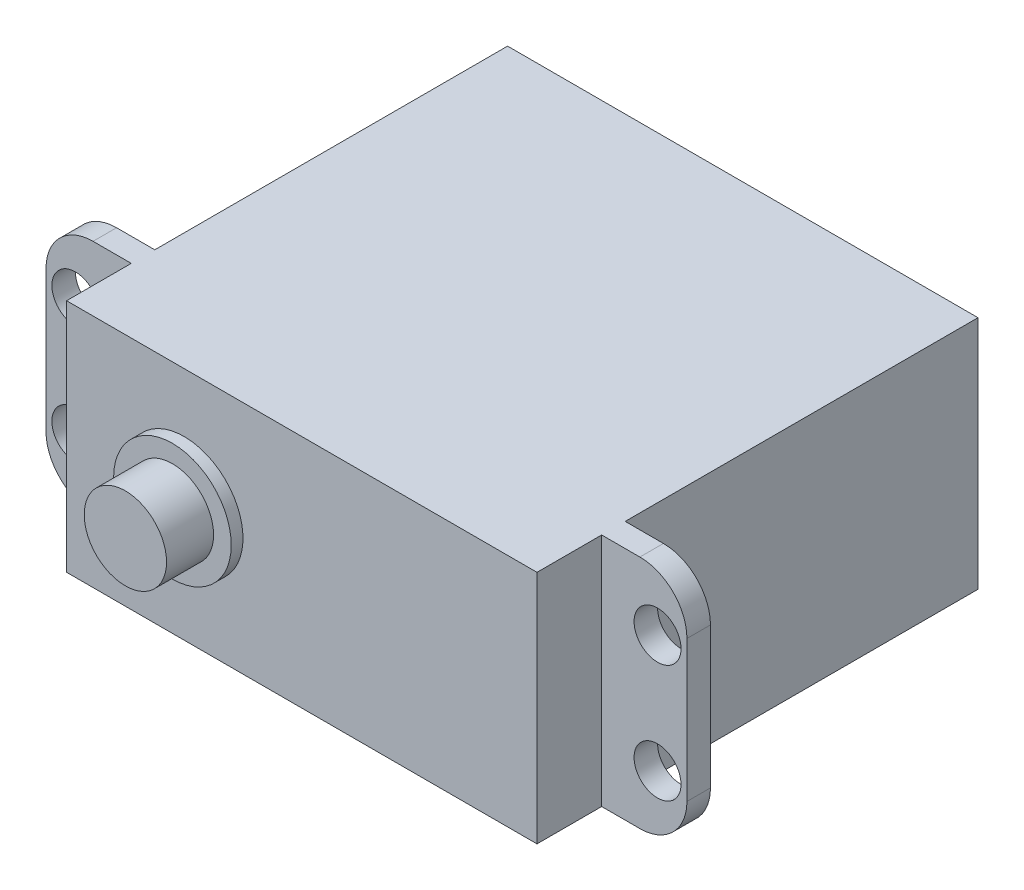
SolidWorks part; units mm, degrees
ref_plane "Front Plane" through (0, 0, 0) normal (0, 0, 1) x (1, 0, 0)
ref_plane "Top Plane" through (0, 0, 0) normal (0, 1, 0) x (1, 0, 0)
ref_plane "Right Plane" through (0, 0, 0) normal (1, 0, 0) x (0, 0, -1)
sketch "Sketch1" plane through (0, 0, 0) normal (0, 0, 1) x (1, 0, 0)
  line L1 (-20, -10) -> (20, -10)
  line L2 (-20, -10) -> (-20, 10)
  line L3 (-20, 10) -> (20, 10)
  line L4 (20, -10) -> (20, 10)
  line L5 (-20, -10) -> (20, 10) construction
  line L6 (-20, 10) -> (20, -10) construction
  point P0 (0, 0)
extrude "Boss-Extrude2" add sketch "Sketch1" along normal blind 37.5 contours L3 L4 L1 L2
sketch "Sketch2" plane through (20, 0, 0) normal (1, 0, 0) x (0, 0, -1)
  line L0 (-37.5, -10) -> (-32, -10)
  line L1 (-37.5, -10) -> (0, -10) construction
  line L2 (-32, -10) -> (-32, 10)
  line L3 (-37.5, 10) -> (0, 10) construction
  line L4 (-32, 10) -> (-30, 10)
  line L5 (-30, 10) -> (-30, -10)
  line L6 (-30, -10) -> (-32, -10)
extrude "Boss-Extrude3" add sketch "Sketch2" along normal blind 7.25 contours L2 L4 L5 L6
sketch "Sketch3" plane through (0, 0, 32) normal (0, 0, 1) x (1, 0, 0)
  circle A0 centre (24.75, -4.9991) radius 1.9955
  circle A1 centre (24.75, 4.9994) radius 1.9955
extrude "Cut-Extrude1" cut sketch "Sketch3" against normal blind 2 contours A1 | A0
fillet "Fillet3" radius 4 2 edges at (27.25, 10, 31) (27.25, -10, 31)
sketch "Sketch4" plane through (-20, 0, 0) normal (-1, 0, 0) x (0, 0, 1)
  line L0 (37.5, -10) -> (32, -10)
  line L1 (37.5, -10) -> (0, -10) construction
  line L2 (32, -10) -> (32, 10)
  line L3 (37.5, 10) -> (0, 10) construction
  line L4 (32, 10) -> (30, 10)
  line L5 (30, 10) -> (30, -10)
  line L6 (30, -10) -> (32, -10)
extrude "Boss-Extrude4" add sketch "Sketch4" along normal blind 7.25 contours L2 L4 L5 L6
sketch "Sketch5" plane through (0, 0, 32) normal (0, 0, 1) x (1, 0, 0)
  circle A0 centre (-24.75, 5) radius 2
  circle A1 centre (-24.75, -5) radius 2
extrude "Cut-Extrude2" cut sketch "Sketch5" against normal blind 2
fillet "Fillet4" radius 4 2 edges at (-27.25, -10, 31) (-27.25, 10, 31)
sketch "Sketch6" plane through (0, 0, 37.5) normal (0, 0, 1) x (1, 0, 0)
  circle A1 centre (-10, 0) radius 5
extrude "Boss-Extrude5" add sketch "Sketch6" along normal blind 1
sketch "Sketch7" plane through (0, 0, 38.5) normal (0, 0, 1) x (1, 0, 0)
  circle A0 centre (-10, 0) radius 3.5
extrude "Boss-Extrude7" add sketch "Sketch7" along normal blind 4
